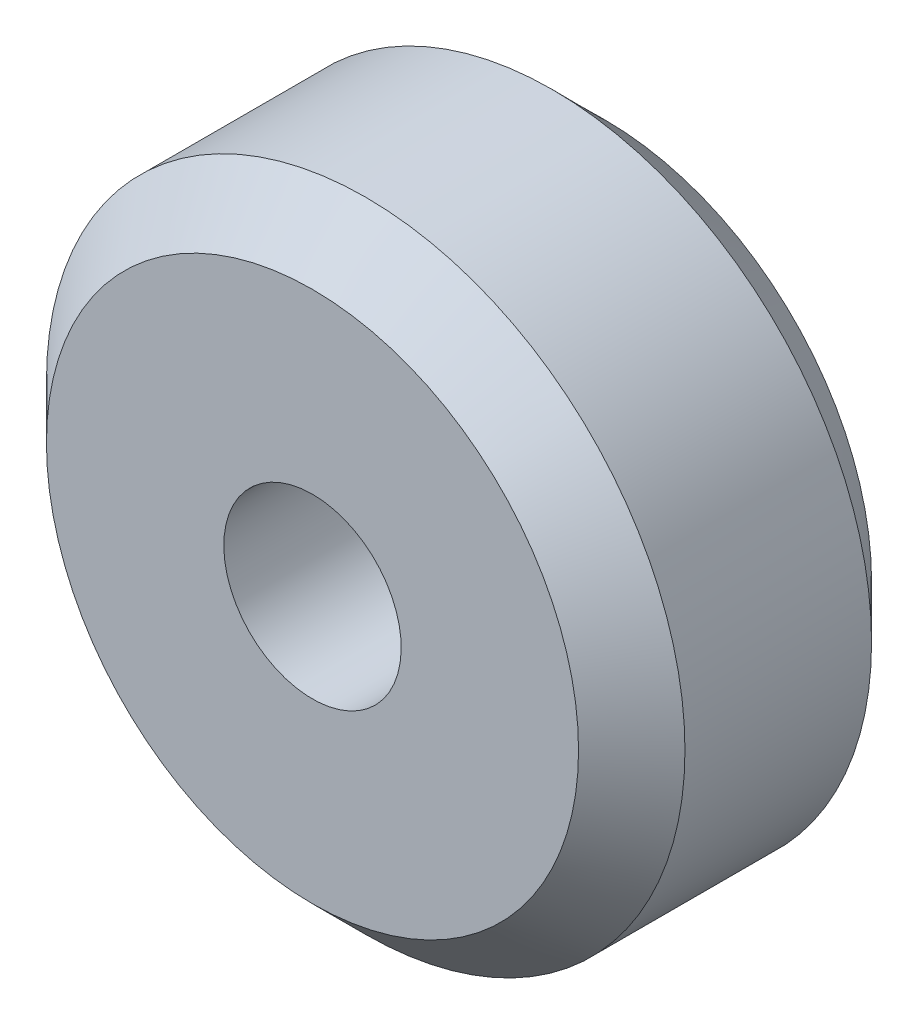
SolidWorks part; units mm, degrees
ref_plane "Front Plane" through (0, 0, 0) normal (0, 0, 1) x (1, 0, 0)
ref_plane "Top Plane" through (0, 0, 0) normal (0, 1, 0) x (1, 0, 0)
ref_plane "Right Plane" through (0, 0, 0) normal (1, 0, 0) x (0, 0, -1)
sketch "Sketch1" plane through (0, 0, 0) normal (1, 0, 0) x (0, 0, -1)
  line L0 (0, 0) -> (5.26, 0)
  line L1 (-1.5, 1.5) -> (-1.5, 9)
  line L2 (6.76, 1.5) -> (6.76, 9)
  line L3 (0, 0) -> (-1.5, 1.5)
  line L4 (5.26, 0) -> (6.76, 1.5)
  line L5 (-1.5, 9) -> (6.76, 9)
  dimension "D1" = 5.26
  dimension "D2" = 7.5
  dimension "D3" = 135
  dimension "D4" = 1.5
revolve "Revolve1" add sketch "Sketch1" angle 360 about L5
sketch "Sketch2" plane through (0, 0, -6.76) normal (0, 0, -1) x (-1, 0, 0)
  circle A0 centre (0, 9) radius 2.5
  dimension "D1" = 5
extrude "Cut-Extrude1" cut sketch "Sketch2" against normal through all
